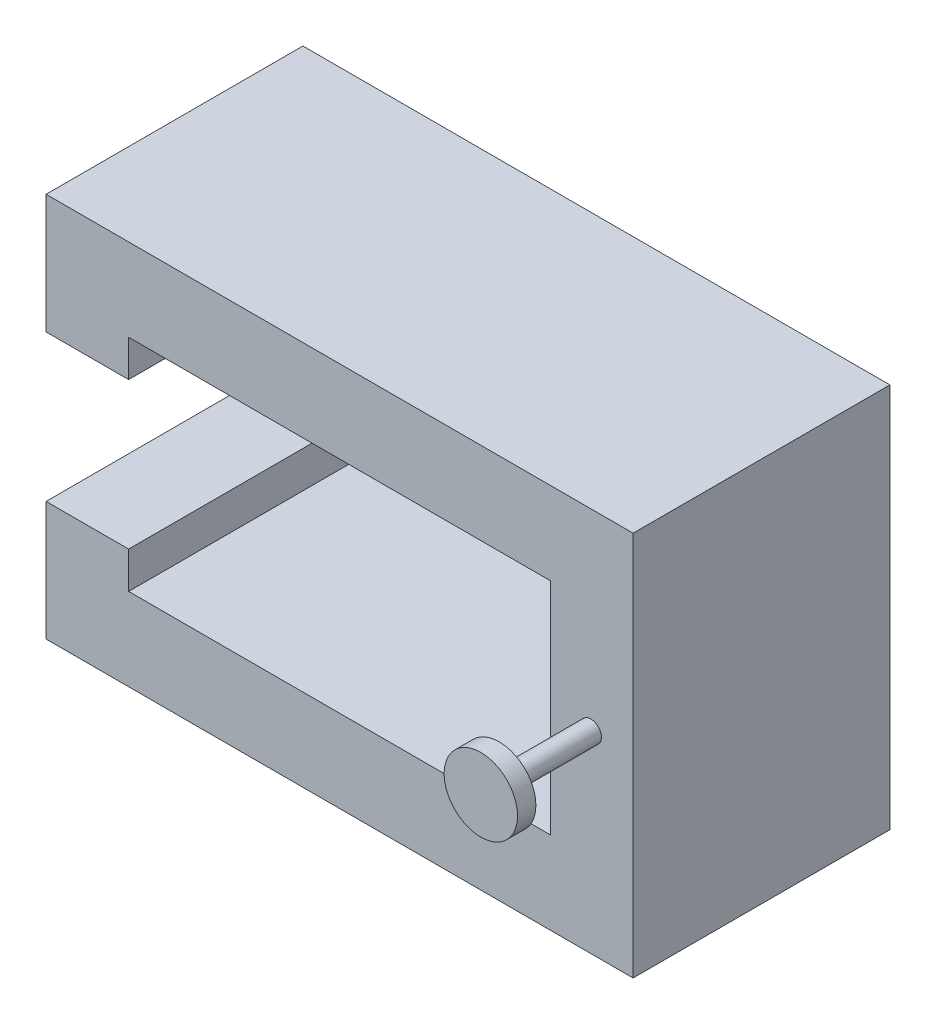
SolidWorks part; units mm, degrees
ref_plane "Front Plane" through (0, 0, 0) normal (0, 0, 1) x (1, 0, 0)
ref_plane "Top Plane" through (0, 0, 0) normal (0, 1, 0) x (1, 0, 0)
ref_plane "Right Plane" through (0, 0, 0) normal (1, 0, 0) x (0, 0, -1)
sketch "Sketch1" plane through (0, 0, 0) normal (0, 0, 1) x (1, 0, 0)
  line L1 (0, 0) -> (32, 0)
  line L2 (0, 0) -> (0, 6.5)
  line L3 (0, 21) -> (32, 21)
  line L4 (32, 0) -> (32, 21)
  line L5 (0, 14.5) -> (4.5, 14.5)
  line L6 (16, 21) -> (16, 16.5)
  line L7 (16, 0) -> (16, 4.5)
  line L8 (0, 6.5) -> (4.5, 6.5)
  line L9 (27.5, 4.5) -> (4.5, 4.5)
  line L10 (27.5, 4.5) -> (27.5, 16.5)
  line L11 (27.5, 16.5) -> (4.5, 16.5)
  line L12 (4.5, 4.5) -> (4.5, 6.5)
  line L15 (0, 14.5) -> (0, 21)
  line L16 (4.5, 14.5) -> (4.5, 16.5)
  dimension "D1" = 32
  dimension "D2" = 21
  dimension "D3" = 2
  dimension "D5" = 4.5
  dimension "D6" = 4.5
  dimension "D7" = 23
  dimension "D8" = 12
  dimension "D9" = 6.364
  dimension "D10" = 6.364
  dimension "D11" = 2
extrude "Boss-Extrude3" add sketch "Sketch1" along normal blind 14
sketch "Sketch4" plane through (0, 0, 14) normal (0, 0, 1) x (1, 0, 0)
  line L0 (32, 10.5) -> (29.7, 10.5)
  line L1 (32, 0) -> (32, 21) construction
  circle A0 centre (29.7, 10.5) radius 0.575
  dimension "D2" = 1.15
  dimension "D1" = 2.3
extrude "Boss-Extrude4" add sketch "Sketch4" along normal blind 5
sketch "Sketch5" plane through (0, 0, 19) normal (0, 0, 1) x (1, 0, 0)
  circle A0 centre (29.7, 10.5) radius 2
  dimension "D1" = 4
extrude "Boss-Extrude5" add sketch "Sketch5" along normal blind 1
